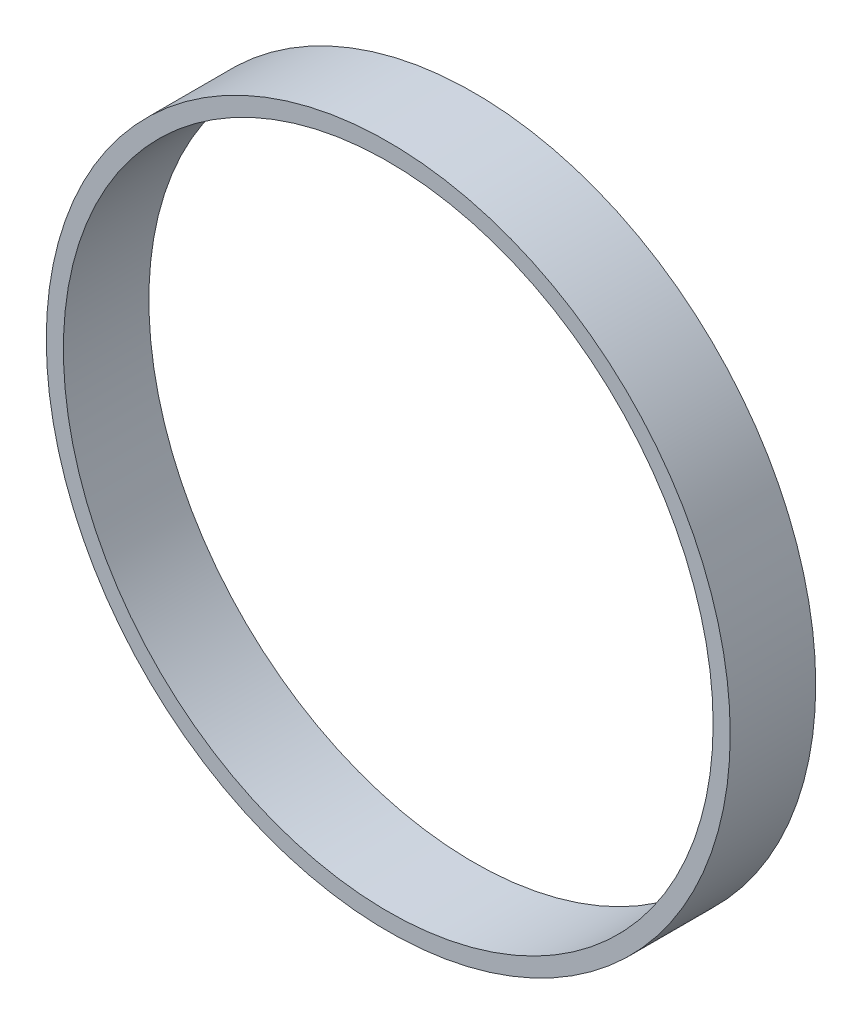
SolidWorks part; units mm, degrees
material "1060 Alloy"
ref_plane "Front Plane" through (0, 0, 0) normal (0, 0, 1) x (1, 0, 0)
ref_plane "Top Plane" through (0, 0, 0) normal (0, 1, 0) x (1, 0, 0)
ref_plane "Right Plane" through (0, 0, 0) normal (1, 0, 0) x (0, 0, -1)
sketch "Sketch1" plane through (0, 0, 0) normal (0, 0, 1) x (1, 0, 0)
  circle A0 centre (0, 0) radius 25 construction
  circle A1 centre (0, 0) radius 40
  circle A2 centre (0, 0) radius 38
  dimension "D1" = 50
  dimension "D2" = 80
  dimension "D3" = 2
extrude "Boss-Extrude1" add sketch "Sketch1" along normal blind 10
